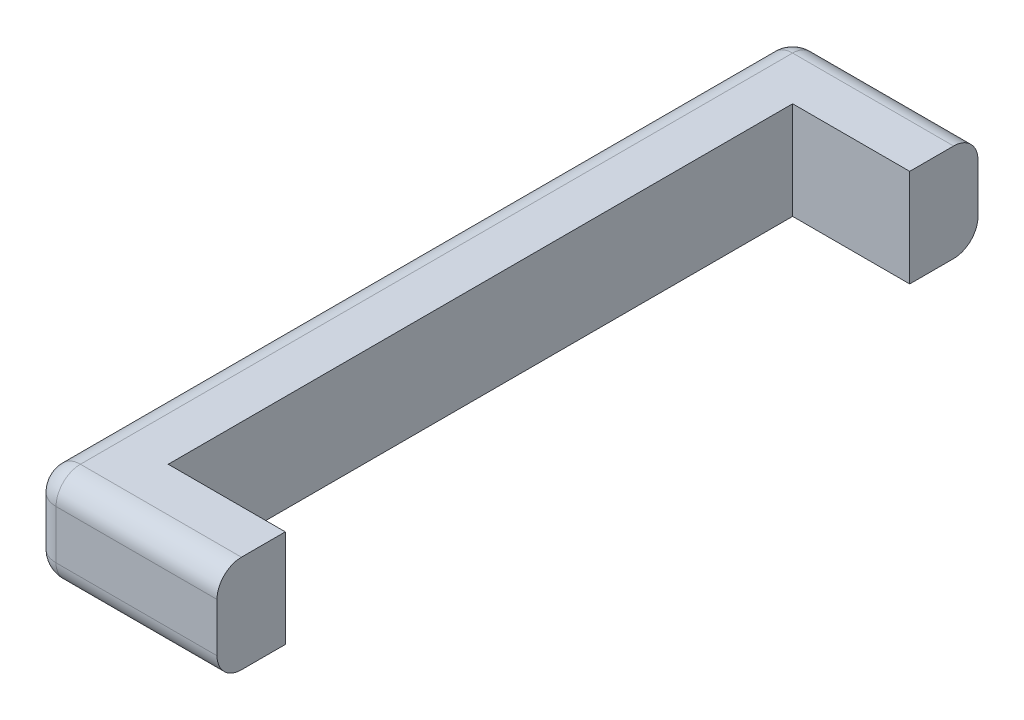
SolidWorks part; units mm, degrees
ref_plane "Front Plane" through (0, 0, 0) normal (0, 0, 1) x (1, 0, 0)
ref_plane "Top Plane" through (0, 0, 0) normal (0, 1, 0) x (1, 0, 0)
ref_plane "Right Plane" through (0, 0, 0) normal (1, 0, 0) x (0, 0, -1)
sketch "Sketch2" plane through (0, 0, 0) normal (0, 1, 0) x (1, 0, 0)
  line L0 (241.3, -406.4) -> (241.3, -495.3)
  line L1 (0, 495.3) -> (241.3, 495.3)
  line L2 (0, 495.3) -> (0, -495.3)
  line L3 (0, -495.3) -> (241.3, -495.3)
  line L4 (241.3, 495.3) -> (241.3, 406.4)
  line L5 (241.3, 406.4) -> (88.9, 406.4)
  line L7 (241.3, -406.4) -> (88.9, -406.4)
  line L8 (88.9, 406.4) -> (88.9, -406.4)
  dimension "D1" = 812.8
  dimension "D2" = 152.4
  dimension "D3" = 88.9
  dimension "D4" = 88.9
extrude "Boss-Extrude1" add sketch "Sketch2" along normal mid plane 127
fillet "Fillet1" radius 31.75 2 edges at (0, 0, -495.3) (0, 0, 495.3)
fillet "Fillet2" radius 31.75 10 edges at (136.525, -63.5, -495.3) (9.2994, -63.5, -486.0006) (136.525, -63.5, 495.3) (9.2994, -63.5, 486.0006) (136.525, 63.5, -495.3) (9.2994, 63.5, -486.0006) (136.525, 63.5, 495.3) (9.2994, 63.5, 486.0006) (0, -63.5, 0) (0, 63.5, 0)
